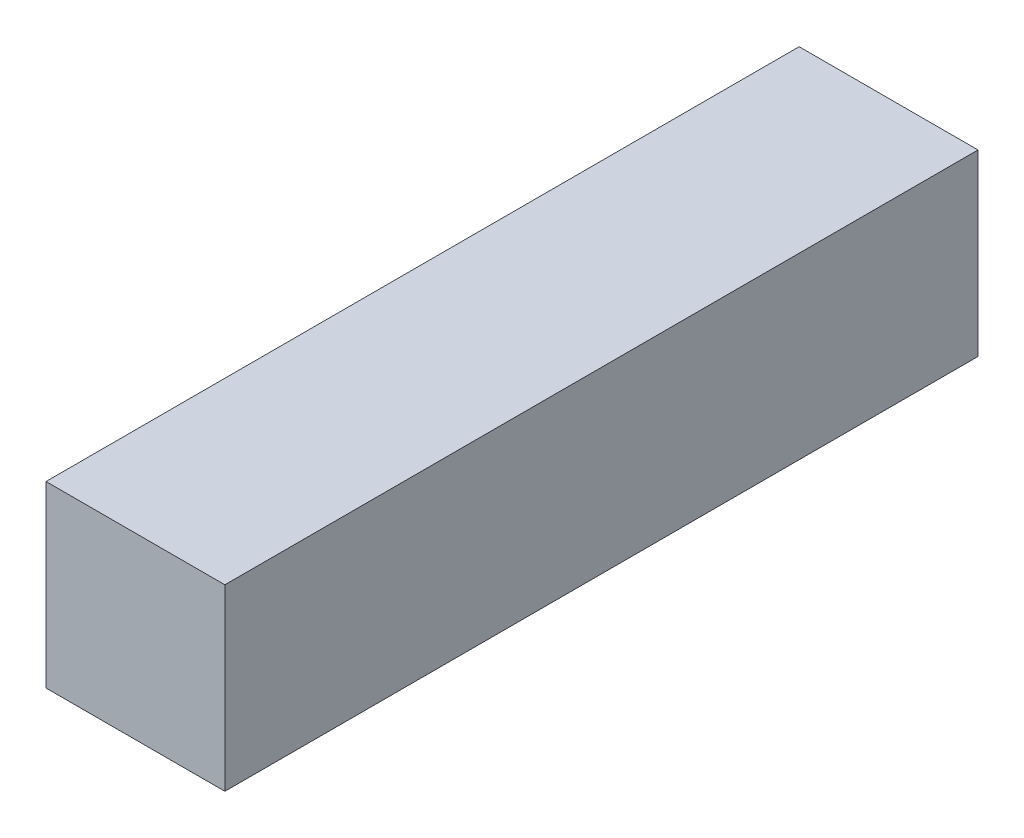
SolidWorks part; units mm, degrees
material "Stainless Steel (ferritic)"
ref_plane "Front Plane" through (0, 0, 0) normal (0, 0, 1) x (1, 0, 0)
ref_plane "Top Plane" through (0, 0, 0) normal (0, 1, 0) x (1, 0, 0)
ref_plane "Right Plane" through (0, 0, 0) normal (1, 0, 0) x (0, 0, -1)
sketch "Sketch1" plane through (0, 0, 0) normal (0, 0, 1) x (1, 0, 0)
  line L1 (-9.5, -9.5) -> (9.5, -9.5)
  line L2 (-9.5, -9.5) -> (-9.5, 9.5)
  line L3 (-9.5, 9.5) -> (9.5, 9.5)
  line L4 (9.5, -9.5) -> (9.5, 9.5)
  line L5 (-9.5, -9.5) -> (9.5, 9.5) construction
  line L6 (-9.5, 9.5) -> (9.5, -9.5) construction
  point P0 (0, 0)
extrude "Boss-Extrude1" add sketch "Sketch1" along normal blind 80
